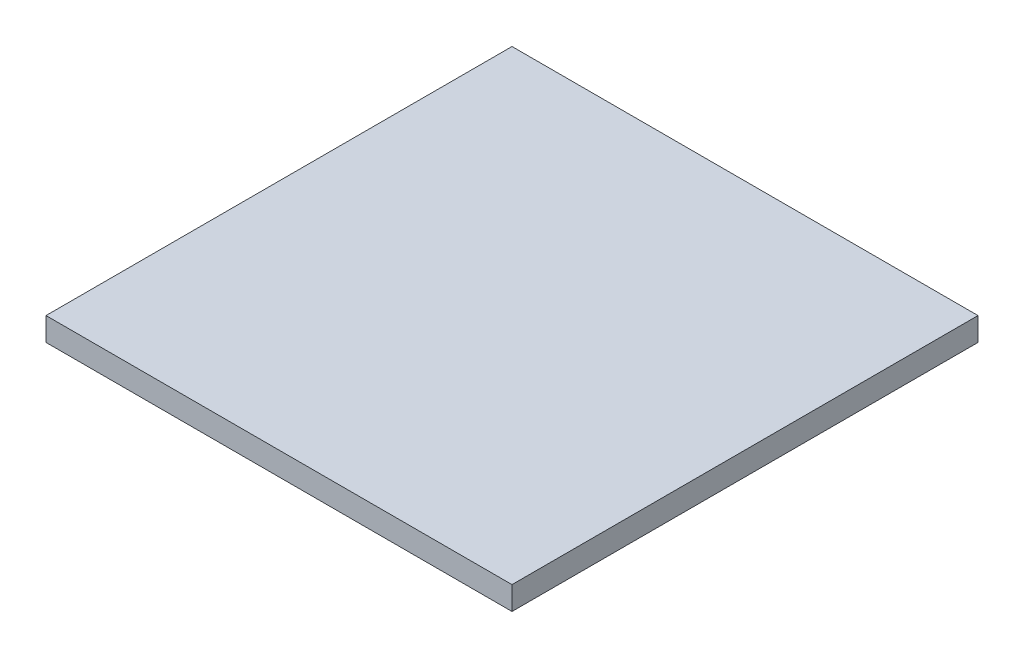
SolidWorks part; units mm, degrees
material "paste"
ref_plane "Front Plane" through (0, 0, 0) normal (0, 0, 1) x (1, 0, 0)
ref_plane "Top Plane" through (0, 0, 0) normal (0, 1, 0) x (1, 0, 0)
ref_plane "Right Plane" through (0, 0, 0) normal (1, 0, 0) x (0, 0, -1)
sketch "Sketch2" plane through (0, 0, 0) normal (0, 1, 0) x (1, 0, 0)
  line L0 (-18.6294, 11.9402) -> (1.3706, 11.9402)
  line L1 (-18.6294, 11.9402) -> (-18.6294, -8.0598)
  line L2 (-18.6294, -8.0598) -> (1.3706, -8.0598)
  line L3 (1.3706, 11.9402) -> (1.3706, -8.0598)
extrude "Boss-Extrude1" add sketch "Sketch2" along normal blind 1
